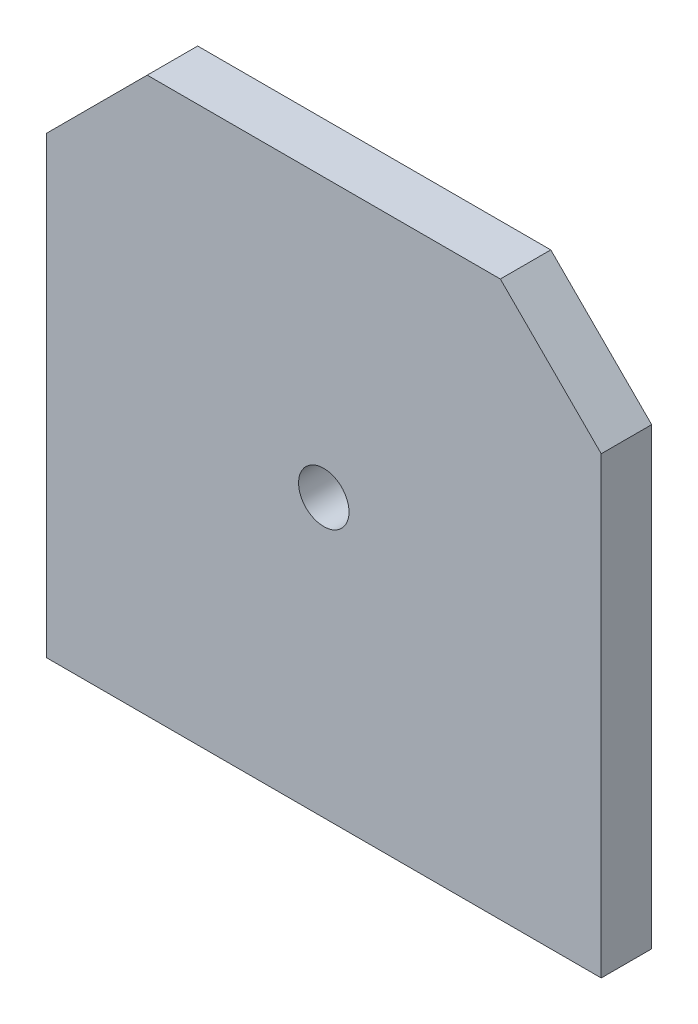
SolidWorks part; units mm, degrees
ref_plane "Ön Düzlem" through (0, 0, 0) normal (0, 0, 1) x (1, 0, 0)
ref_plane "Üst Düzlem" through (0, 0, 0) normal (0, 1, 0) x (1, 0, 0)
ref_plane "Sağ Düzlem" through (0, 0, 0) normal (1, 0, 0) x (0, 0, -1)
sketch "Sketch1" plane through (0, 0, 0) normal (0, 0, 1) x (1, 0, 0)
  line L0 (-27.5, 17.5) -> (-17.5, 27.5)
  line L1 (-17.5, 27.5) -> (17.5, 27.5)
  line L2 (-27.5, 17.5) -> (-27.5, -27.5)
  line L3 (-27.5, -27.5) -> (27.5, -27.5)
  line L4 (27.5, 17.5) -> (27.5, -27.5)
  line L5 (-22.5, 22.5) -> (27.5, -27.5) construction
  line L6 (-27.5, -27.5) -> (22.5, 22.5) construction
  line L7 (17.5, 27.5) -> (27.5, 17.5)
  circle A0 centre (0, 0) radius 2.5
  point P0 (0, 0)
  dimension "D1" = 5
extrude "Boss-Extrude1" add sketch "Sketch1" along normal blind 5
